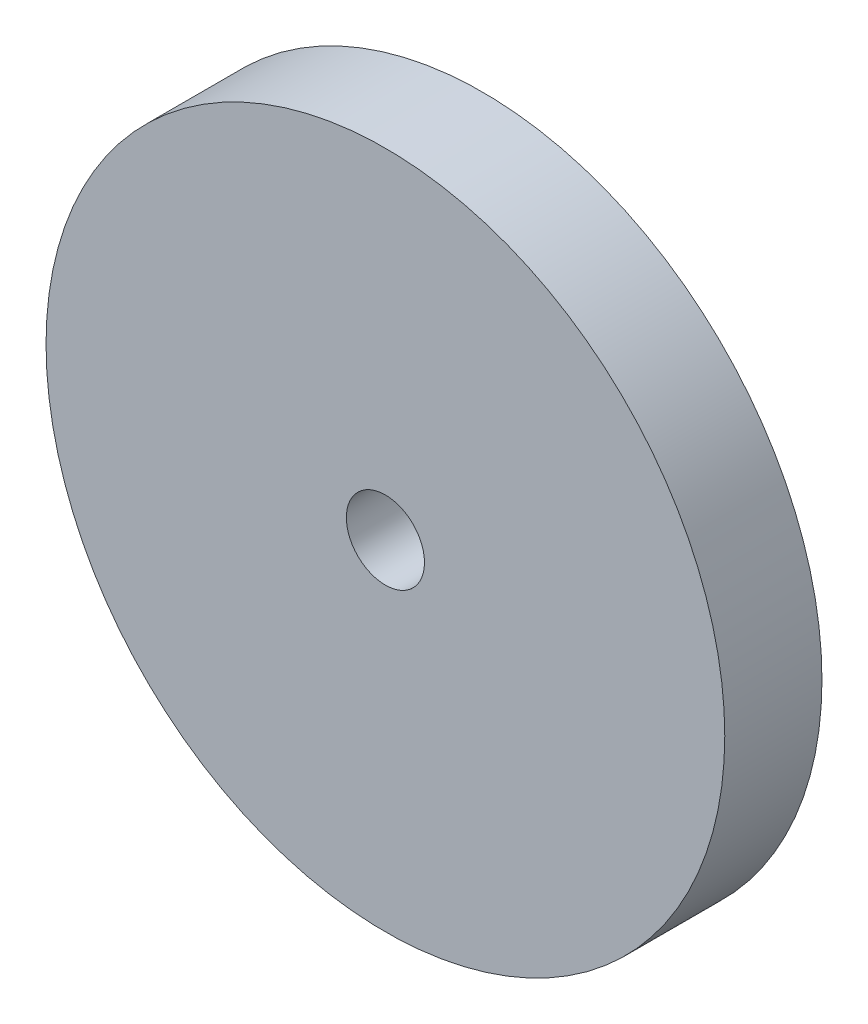
SolidWorks part; units mm, degrees
ref_plane "Front Plane" through (0, 0, 0) normal (0, 0, 1) x (1, 0, 0)
ref_plane "Top Plane" through (0, 0, 0) normal (0, 1, 0) x (1, 0, 0)
ref_plane "Right Plane" through (0, 0, 0) normal (1, 0, 0) x (0, 0, -1)
sketch "Sketch1" plane through (0, 0, 0) normal (0, 0, 1) x (1, 0, 0)
  circle A0 centre (0, 0) radius 22.175
  circle A1 centre (0, 0) radius 2.5527
  dimension "D1" = 44.35
  dimension "D2" = 5.1054
extrude "Boss-Extrude1" add sketch "Sketch1" along normal blind 6.35
